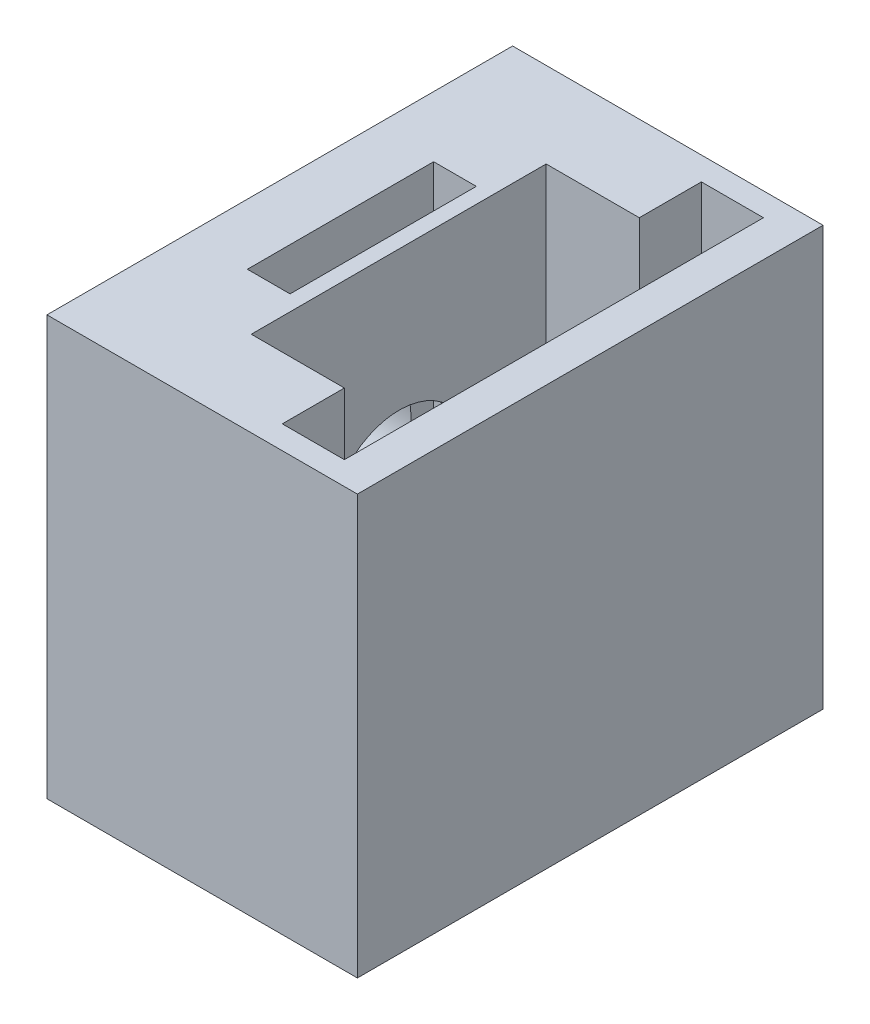
SolidWorks part; units mm, degrees
ref_plane "Front Plane" through (0, 0, 0) normal (0, 0, 1) x (1, 0, 0)
ref_plane "Top Plane" through (0, 0, 0) normal (0, 1, 0) x (1, 0, 0)
ref_plane "Right Plane" through (0, 0, 0) normal (1, 0, 0) x (0, 0, -1)
sketch "Sketch2" plane through (0, 0, 0) normal (1, 0, 0) x (0, 0, -1)
  line L1 (0, 0) -> (30, 0)
  line L2 (0, 0) -> (0, 27)
  line L3 (0, 27) -> (30, 27)
  line L4 (30, 0) -> (30, 27)
  dimension "D1" = 30
  dimension "D2" = 27
extrude "Boss-Extrude1" add sketch "Sketch2" along normal blind 20
sketch "Sketch6" plane through (2.2961, 27, -0.2935) normal (0, 1, 0) x (1, 0, 0)
  line L0 (17.7039, 29.7065) -> (-2.2961, 29.7065) construction
  line L5 (11.3658, 28.2065) -> (15.3658, 28.2065)
  line L6 (11.3658, 28.2065) -> (11.3658, 1.2065)
  line L7 (11.3658, 1.2065) -> (15.3658, 1.2065)
  line L8 (15.3658, 28.2065) -> (15.3658, 1.2065)
  dimension "D1" = 4
  dimension "D2" = 27
  dimension "D3" = 1.5
extrude "Cut-Extrude4" cut sketch "Sketch6" against normal blind 26 contours L8 L7 L6 L5
sketch "Sketch9" plane through (0, 27, 0) normal (0, 1, 0) x (1, 0, 0)
  line L0 (13.662, 28.5) -> (13.662, 1.5) construction
  line L1 (7.662, 24.5) -> (13.662, 24.5)
  line L2 (7.662, 24.5) -> (7.662, 5.5)
  line L3 (7.662, 5.5) -> (13.662, 5.5)
  line L4 (13.662, 24.5) -> (13.662, 5.5)
  line L5 (13.662, 28.5) -> (17.662, 28.5) construction
  line L6 (13.662, 1.5) -> (17.662, 1.5) construction
  dimension "D1" = 4
  dimension "D2" = 4
  dimension "D3" = 6
extrude "Cut-Extrude5" cut sketch "Sketch9" against normal blind 20
sketch "Sketch11" plane through (0, 0, 0) normal (-1, 0, 0) x (0, 0, 1)
  line L0 (-30, 27) -> (0, 27) construction
  line L1 (-30, 0) -> (-30, 27) construction
  circle A0 centre (-15.1, 13.5) radius 5
  dimension "D1" = 13.5
  dimension "D2" = 14.9
extrude "Cut-Extrude8" cut sketch "Sketch11" against normal blind 0.5
sketch "Sketch12" plane through (0, 27, 0) normal (0, 1, 0) x (1, 0, 0)
  line L0 (7.662, 24.5) -> (7.662, 5.5) construction
  line L1 (3.912, 21) -> (6.662, 21)
  line L2 (3.912, 21) -> (3.912, 9)
  line L3 (3.912, 9) -> (6.662, 9)
  line L4 (6.662, 21) -> (6.662, 9)
  line L6 (13.662, 28.5) -> (17.662, 28.5) construction
  line L7 (13.662, 1.5) -> (17.662, 1.5) construction
  point P6 (5.287, 9)
  point P9 (6.662, 15)
  dimension "D1" = 7.5
  dimension "D2" = 7.5
  dimension "D3" = 2.75
  dimension "D4" = 1
extrude "Cut-Extrude12" cut sketch "Sketch12" against normal blind 17.5
sketch "Sketch15" plane through (0.5, 0, 0) normal (-1, 0, 0) x (0, 0, 1)
  line L0 (-30, 0) -> (-30, 27) construction
  line L1 (-30, 27) -> (0, 27) construction
  circle A0 centre (-15.04, 13.5) radius 4.5
  dimension "D1" = 14.96
  dimension "D2" = 13.5
extrude "Cut-Extrude13" cut sketch "Sketch15" against normal blind 10
sketch "Sketch16" plane through (0, 0, 0) normal (0, 0, 1) x (1, 0, 0)
